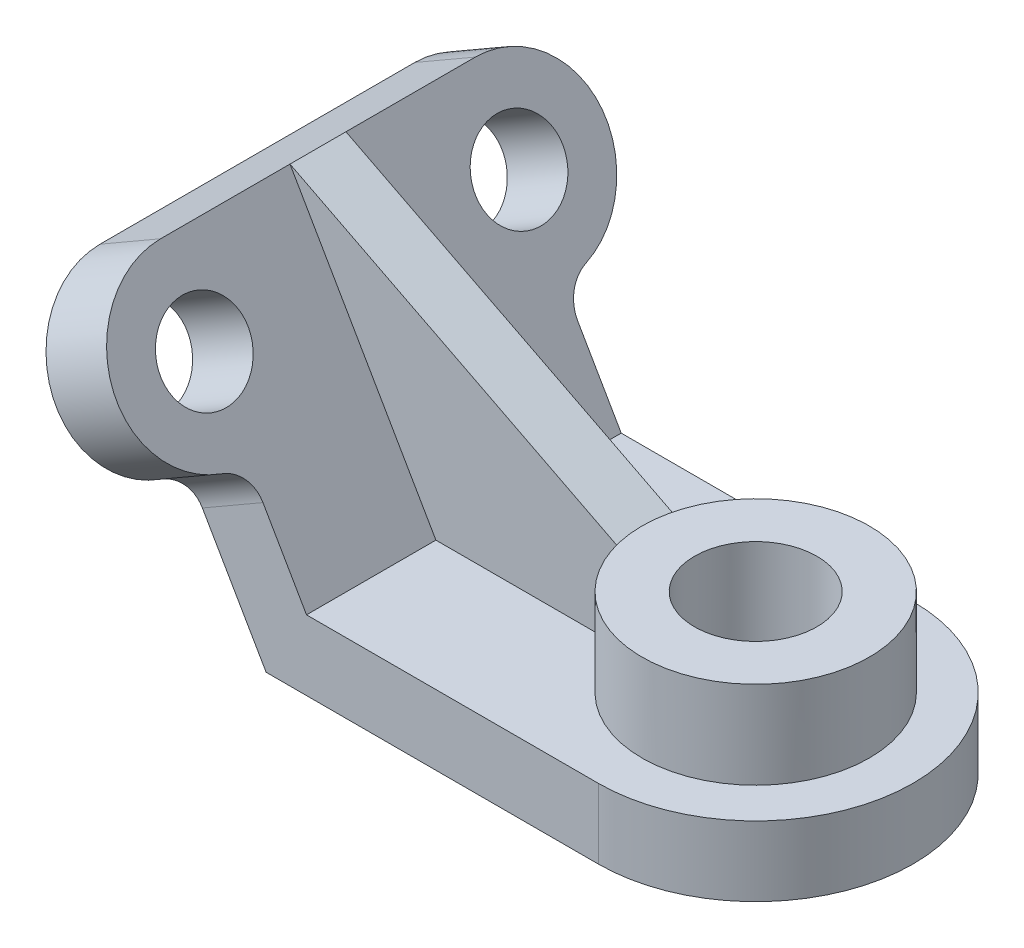
SolidWorks part; units mm, degrees
ref_plane "Front Plane" through (0, 0, 0) normal (0, 0, 1) x (1, 0, 0)
ref_plane "Top Plane" through (0, 0, 0) normal (0, 1, 0) x (1, 0, 0)
ref_plane "Right Plane" through (0, 0, 0) normal (1, 0, 0) x (0, 0, -1)
sketch "Sketch1" plane through (0, 0, 0) normal (0, 0, 1) x (1, 0, 0)
  line L0 (0, 0) -> (95, 0)
  line L1 (95, 0) -> (95, 20)
  line L2 (95, 20) -> (11.547, 20)
  line L3 (11.547, 20) -> (-30.1795, 92.2724)
  line L4 (-30.1795, 92.2724) -> (-47.5, 82.2724)
  line L5 (-47.5, 82.2724) -> (0, 0)
  point P6 (0, 0)
  point P8 (0, 0)
  dimension "D1" = 120
  dimension "D2" = 20
  dimension "D3" = 95
  dimension "D4" = 95
  dimension "D5" = 20
extrude "Boss-Extrude1" add sketch "Sketch1" against normal mid plane 90
sketch "Sketch2" plane through (17.3205, 10, 0) normal (0.866, 0.5, 0) x (0, 0, -1)
  line L1 (-45, 95) -> (-45, 70)
  line L2 (-45, 95) -> (-45, 45)
  line L3 (45, 11.547) -> (45, 95) construction
  line L4 (45, 95) -> (45, 45)
  arc A1 (-45, 95) -> (-45, 45) centre (-45, 70) ccw
  arc A2 (45, 45) -> (45, 95) centre (45, 70) ccw
  line M1 (-45, 95) -> (-45, 11.547)
  line M3 (45, 11.547) -> (45, 95)
  dimension "D1" = 50
extrude "Boss-Extrude2" add sketch "Sketch2" against normal blind 20 contours A1 M1 | A2 M3
sketch "Sketch3" plane through (17.3205, 10, 0) normal (0.866, 0.5, 0) x (0, 0, -1)
  circle A0 centre (-45, 70) radius 12.5
  circle A1 centre (45, 70) radius 12.5
  dimension "D1" = 25
extrude "Cut-Extrude1" cut sketch "Sketch3" against normal blind 20
sketch "Sketch4" plane through (0, 20, 0) normal (0, 1, 0) x (1, 0, 0)
  line L0 (95, 45) -> (95, -45) construction
  line L1 (95, 45) -> (95, -45)
  arc A0 (95, -45) -> (95, 45) centre (95, 0) ccw
extrude "Boss-Extrude3" add sketch "Sketch4" against normal blind 20
sketch "Sketch5" plane through (0, 20, 0) normal (0, 1, 0) x (1, 0, 0)
  circle A0 centre (95, 0) radius 32.5
  circle A1 centre (95, 0) radius 17.5
extrude "Boss-Extrude4" add sketch "Sketch5" along normal blind 25
fillet "Fillet1" radius 10 2 edges at (-13.8397, 43.9711, -45) (-13.8397, 43.9711, 45)
sketch "Sketch8" plane through (0, 0, 0) normal (0, -1, 0) x (-1, 0, 0)
  circle A0 centre (-95, 0) radius 17.5
extrude "Cut-Extrude2" cut sketch "Sketch8" against normal through all
sketch "Sketch9" plane through (0, 0, 0) normal (0, 0, 1) x (1, 0, 0)
  line L0 (-30.1795, 92.2724) -> (62.5, 45)
rib "Rib2" sketch "Sketch9" sketch "Sketch9" thickness 16 extrusion direction parallel to sketch draft on no parameters "D1"=16
